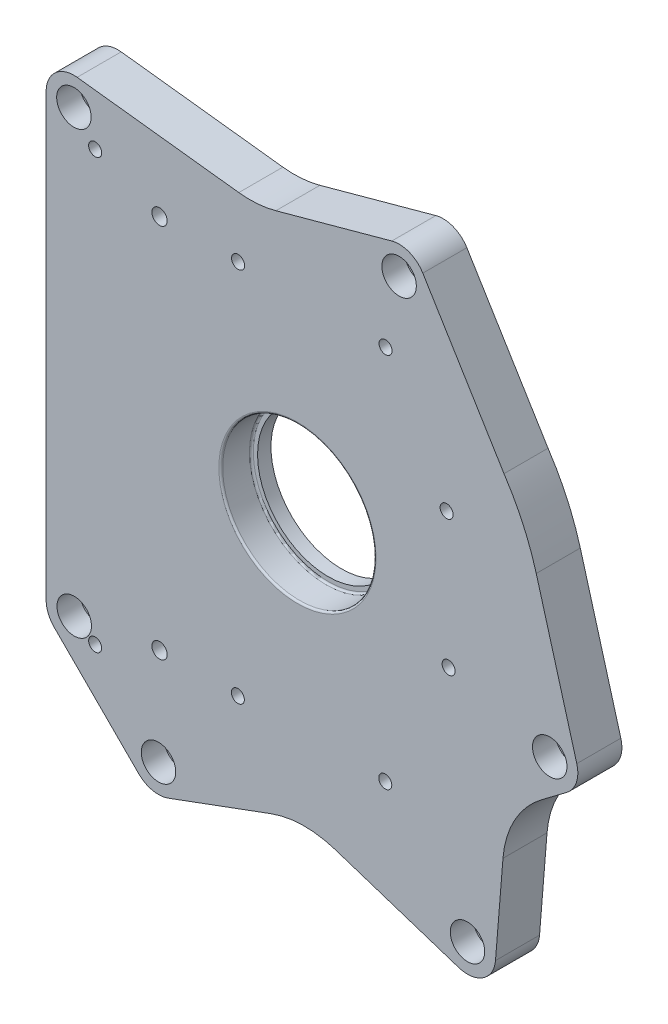
SolidWorks part; units mm, degrees
material "6061-T6 (SS)"
ref_plane "Front Plane" through (0, 0, 0) normal (0, 0, 1) x (1, 0, 0)
ref_plane "Top Plane" through (0, 0, 0) normal (0, 1, 0) x (1, 0, 0)
ref_plane "Right Plane" through (0, 0, 0) normal (1, 0, 0) x (0, 0, -1)
sketch "Sketch1" plane through (0, 0, 0) normal (0, 0, 1) x (1, 0, 0)
  line L0 (84.2211, -163.4901) -> (2.6993, -136.8316)
  line L1 (-67.4584, -162.7302) -> (2.6993, -136.8316)
  line L2 (-82.9108, -159.3414) -> (-126.9141, -115.3364)
  line L3 (140.5448, -56.1387) -> (109.1493, -79.774)
  line L4 (103.4012, -150.7323) -> (109.1493, -79.774)
  line L5 (145.8454, -40.4558) -> (124.6838, 34.9416)
  line L6 (65.4504, 141.1198) -> (107.841, 71.6428)
  line L9 (49.2431, 147.5528) -> (-20.7968, 128.3749)
  line L13 (-115.0226, 139.4368) -> (-20.7968, 128.3749)
  line L14 (-131.2133, 125.0355) -> (-131.2102, -104.9645)
  arc A2 (-115.0226, 139.4368) -> (-131.2133, 125.0355) centre (-116.7133, 125.0357) ccw
  circle A3 centre (-116.7133, 125.0357) radius 3.5 construction
  arc A6 (65.4504, 141.1198) -> (49.2431, 147.5528) centre (53.0725, 133.5676) ccw
  circle A7 centre (-76.5534, 103.7539) radius 2.5 construction
  arc A9 (-131.2102, -104.9645) -> (-126.9141, -115.3364) centre (-116.5415, -104.9643) ccw
  circle A10 centre (-116.5415, -104.9643) radius 3.5 construction
  arc A12 (-82.9108, -159.3414) -> (-67.4584, -162.7302) centre (-72.5383, -148.9692) ccw
  circle A13 centre (-72.5383, -148.9692) radius 3.5 construction
  arc A15 (84.2211, -163.4901) -> (103.4012, -150.7323) centre (88.7803, -149.548) ccw
  arc A17 (140.5448, -56.1387) -> (145.8454, -40.4558) centre (131.7224, -44.4197) ccw
  circle A18 centre (59.1026, -114.9804) radius 2.5 construction
  circle A23 centre (88.7803, -149.548) radius 3.5 construction
  circle A27 centre (131.7224, -44.4197) radius 3.5 construction
  arc A30 (124.6838, 34.9416) -> (107.841, 71.6428) centre (-0.017, -0.0702) ccw
  circle A31 centre (53.0725, 133.5676) radius 3.5 construction
  dimension "D1" = 14.5
  dimension "D2" = 7
  dimension "D3" = 5
extrude "Boss-Extrude1" add sketch "Sketch1" along normal blind 23 contours L5 A30 L6 A6 L9 L13 A2 L14 A9 L2 A12 L1 L0 A15 L4 L3 A17 A31 A3 A7 A10 A13 A18 A23 A27
fillet "Fillet2" radius 50.8 3 edges at (-20.7968, 128.3749, 11.5) (109.1493, -79.774, 11.5) (2.6993, -136.8316, 11.5)
sketch "Sketch2" plane through (0, 0, 23) normal (0, 0, -1) x (-1, 0, 0)
  circle A0 centre (0, 0) radius 40.05
  dimension "D1" = 80.1
extrude "Cut-Extrude1" cut sketch "Sketch2" along normal blind 16
sketch "Sketch5" plane through (0, 0, 23) normal (0, 0, -1) x (-1, 0, 0)
  circle A0 centre (0, 0) radius 36.83
  dimension "D1" = 73.66
extrude "Cut-Extrude2" cut sketch "Sketch5" along normal blind 25.4
sketch "Sketch6" [suppressed] plane through (0, 0, 0) normal (0, 0, 1) x (1, 0, 0)
  circle A0 centre (0, 0) radius 50.8 construction
  point P14 (0, 0)
  dimension "D2" = 101.6
fillet "Fillet5" radius 1 1 edges at (-40.05, 0, 23)
fillet "Fillet6" radius 1 1 edges at (-40.05, 0, 7)
sketch "Sketch43" plane through (0, 0, 23) normal (0, 0, 1) x (1, 0, 0)
  line L13 (0, 0) -> (150.4649, 0) construction
  line L14 (-31.12, -98.35) -> (-105.6166, -112.2929) construction
  line L15 (-31, 98) -> (-105.6166, 111.6261) construction
  line L16 (-105.6166, -112.2929) -> (-105.6166, 111.6261) construction
  line L17 (0, 0) -> (-105.6166, 111.6261) construction
  line L18 (-31, 98) -> (0, 0) construction
  line L19 (0, 0) -> (46, 97.92) construction
  line L20 (77.9, 39.75) -> (0, 0) construction
  line L21 (0, 0) -> (-72, -98.1221) construction
  line L22 (0, 0) -> (78.925, -30.46) construction
  line L23 (45.85, -98.52) -> (0, 0) construction
  line L24 (0, 0) -> (-72, 97.9779) construction
  line L25 (0, 0) -> (-31.12, -98.35) construction
  line L26 (-105.6166, -112.2929) -> (0, 0) construction
  circle A8 centre (0, 0) radius 46.4211 construction
  circle A12 centre (-46.643, -71.23) radius 11.3319 construction
  circle A13 centre (-72, 97.9779) radius 3.9701
  circle A14 centre (-72, -98.1221) radius 3.9701
  circle A15 centre (-105.6166, 111.6261) radius 3
  circle A16 centre (-31, 98) radius 3
  circle A17 centre (46, 97.92) radius 3
  circle A18 centre (77.9, 39.75) radius 3
  circle A19 centre (78.925, -30.46) radius 3
  circle A20 centre (45.85, -98.52) radius 3
  circle A21 centre (-31.12, -98.35) radius 3
  circle A22 centre (-105.6166, -112.2929) radius 3
  circle A23 centre (0, 0) radius 36.83 construction
  dimension "D2" = 45.85
  dimension "D3" = 31.12
  dimension "D1" = 98.52
  dimension "D4" = 98.35
  dimension "D5" = 98.1221
  dimension "D6" = 72
  dimension "D7" = 105.6166
  dimension "D8" = 105.6166
  dimension "D9" = 72
  dimension "D10" = 31
  dimension "D11" = 46
  dimension "D12" = 77.9
  dimension "D13" = 78.925
  dimension "D14" = 39.75
  dimension "D15" = 30.46
  dimension "D16" = 97.92
  dimension "D17" = 98
  dimension "D18" = 97.9779
  dimension "D19" = 111.6261
  dimension "D20" = 112.2929
  dimension "D21" = 196.1
  dimension "D22" = 7.9403
  dimension "D23" = 6
sketch "Sketch59" plane through (0, 0, 23) normal (0, 0, 1) x (1, 0, 0)
  line L0 (145.8454, -40.4558) -> (124.6838, 34.9416) construction
  line L1 (140.5448, -56.1387) -> (127.387, -66.0442) construction
  line L2 (103.4012, -150.7323) -> (107.3061, -102.5275) construction
  line L3 (84.2211, -163.4901) -> (19.4993, -142.3254) construction
  line L4 (-67.4584, -162.7302) -> (-13.8824, -142.9527) construction
  line L5 (-82.9108, -159.3414) -> (-126.9141, -115.3364) construction
  line L6 (65.4504, 141.1198) -> (107.841, 71.6428) construction
  line L7 (49.2431, 147.5528) -> (-11.269, 130.9837) construction
  line L8 (-115.0226, 139.4368) -> (-30.608, 129.5267) construction
  line L9 (-131.2133, 125.0355) -> (-131.2102, -104.9645) construction
  line L10 (145.8454, -40.4558) -> (124.6838, 34.9416)
  line L11 (140.5448, -56.1387) -> (127.387, -66.0442)
  line L12 (103.4012, -150.7323) -> (107.3061, -102.5275)
  line L13 (84.2211, -163.4901) -> (19.4993, -142.3254)
  line L14 (-67.4584, -162.7302) -> (-13.8824, -142.9527)
  line L15 (-82.9108, -159.3414) -> (-126.9141, -115.3364)
  line L16 (65.4504, 141.1198) -> (107.841, 71.6428)
  line L17 (49.2431, 147.5528) -> (-11.269, 130.9837)
  line L18 (-115.0226, 139.4368) -> (-30.608, 129.5267)
  line L19 (-131.2133, 125.0355) -> (-131.2102, -104.9645)
  line L30 (49.2431, 147.5528) -> (-20.7968, 128.3749)
  line L31 (107.841, 71.6428) -> (65.4504, 141.1198)
  line L32 (145.8454, -40.4558) -> (124.6838, 34.9416)
  line L33 (109.1493, -79.774) -> (140.5448, -56.1387)
  line L34 (103.4012, -150.7323) -> (109.1493, -79.774)
  line L35 (2.6993, -136.8316) -> (84.2211, -163.4901)
  line L36 (-67.4584, -162.7302) -> (2.6993, -136.8316)
  line L37 (-126.9141, -115.3364) -> (-82.9108, -159.3414)
  line L38 (-131.2133, 125.0355) -> (-131.2102, -104.9645)
  line L39 (-20.7968, 128.3749) -> (-115.0226, 139.4368)
  line L40 (49.2431, 147.5528) -> (-20.7968, 128.3749)
  line L41 (107.841, 71.6428) -> (65.4504, 141.1198)
  line L42 (145.8454, -40.4558) -> (124.6838, 34.9416)
  line L43 (109.1493, -79.774) -> (140.5448, -56.1387)
  line L44 (103.4012, -150.7323) -> (109.1493, -79.774)
  line L45 (2.6993, -136.8316) -> (84.2211, -163.4901)
  line L46 (-67.4584, -162.7302) -> (2.6993, -136.8316)
  line L47 (-126.9141, -115.3364) -> (-82.9108, -159.3414)
  line L48 (-131.2133, 125.0355) -> (-131.2102, -104.9645)
  line L49 (-20.7968, 128.3749) -> (-115.0226, 139.4368)
  arc A0 (124.6838, 34.9416) -> (107.841, 71.6428) centre (-0.017, -0.0702) ccw construction
  arc A1 (140.5448, -56.1387) -> (145.8454, -40.4558) centre (131.7224, -44.4197) ccw construction
  arc A2 (127.387, -66.0442) -> (107.3061, -102.5275) centre (157.9402, -106.6292) ccw construction
  arc A3 (84.2211, -163.4901) -> (103.4012, -150.7323) centre (88.7803, -149.548) ccw construction
  arc A4 (19.4993, -142.3254) -> (-13.8824, -142.9527) centre (3.7099, -190.6093) ccw construction
  arc A5 (-82.9108, -159.3414) -> (-67.4584, -162.7302) centre (-72.5383, -148.9692) ccw construction
  arc A6 (-131.2102, -104.9645) -> (-126.9141, -115.3364) centre (-116.5415, -104.9643) ccw construction
  arc A7 (65.4504, 141.1198) -> (49.2431, 147.5528) centre (53.0725, 133.5676) ccw construction
  arc A8 (-30.608, 129.5267) -> (-11.269, 130.9837) centre (-24.6849, 179.9802) ccw construction
  arc A9 (-115.0226, 139.4368) -> (-131.2133, 125.0355) centre (-116.7133, 125.0357) ccw construction
  arc A10 (124.6838, 34.9416) -> (107.841, 71.6428) centre (-0.017, -0.0702) ccw
  arc A11 (140.5448, -56.1387) -> (145.8454, -40.4558) centre (131.7224, -44.4197) ccw
  arc A12 (127.387, -66.0442) -> (107.3061, -102.5275) centre (157.9402, -106.6292) ccw
  arc A13 (84.2211, -163.4901) -> (103.4012, -150.7323) centre (88.7803, -149.548) ccw
  arc A14 (19.4993, -142.3254) -> (-13.8824, -142.9527) centre (3.7099, -190.6093) ccw
  arc A15 (-82.9108, -159.3414) -> (-67.4584, -162.7302) centre (-72.5383, -148.9692) ccw
  arc A16 (-131.2102, -104.9645) -> (-126.9141, -115.3364) centre (-116.5415, -104.9643) ccw
  arc A17 (65.4504, 141.1198) -> (49.2431, 147.5528) centre (53.0725, 133.5676) ccw
  arc A18 (-30.608, 129.5267) -> (-11.269, 130.9837) centre (-24.6849, 179.9802) ccw
  arc A19 (-115.0226, 139.4368) -> (-131.2133, 125.0355) centre (-116.7133, 125.0357) ccw
  circle A20 centre (-116.7133, 125.0357) radius 3.5 construction
  circle A21 centre (-76.5534, 103.7539) radius 2.5 construction
  circle A22 centre (-116.5415, -104.9643) radius 3.5 construction
  circle A23 centre (-72.5383, -148.9692) radius 3.5 construction
  circle A24 centre (59.1026, -114.9804) radius 2.5 construction
  circle A25 centre (88.7803, -149.548) radius 3.5 construction
  circle A26 centre (131.7224, -44.4197) radius 3.5 construction
  arc A27 (65.4504, 141.1198) -> (49.2431, 147.5528) centre (53.0725, 133.5676) ccw
  arc A28 (124.6838, 34.9416) -> (107.841, 71.6428) centre (-0.017, -0.0702) ccw
  arc A29 (140.5448, -56.1387) -> (145.8454, -40.4558) centre (131.7224, -44.4197) ccw
  arc A30 (84.2211, -163.4901) -> (103.4012, -150.7323) centre (88.7803, -149.548) ccw
  arc A31 (-82.9108, -159.3414) -> (-67.4584, -162.7302) centre (-72.5383, -148.9692) ccw
  arc A32 (-131.2102, -104.9645) -> (-126.9141, -115.3364) centre (-116.5415, -104.9643) ccw
  arc A33 (-115.0226, 139.4368) -> (-131.2133, 125.0355) centre (-116.7133, 125.0357) ccw
  arc A34 (65.4504, 141.1198) -> (49.2431, 147.5528) centre (53.0725, 133.5676) ccw
  arc A35 (124.6838, 34.9416) -> (107.841, 71.6428) centre (-0.017, -0.0702) ccw
  arc A36 (140.5448, -56.1387) -> (145.8454, -40.4558) centre (131.7224, -44.4197) ccw
  arc A37 (84.2211, -163.4901) -> (103.4012, -150.7323) centre (88.7803, -149.548) ccw
  arc A38 (-82.9108, -159.3414) -> (-67.4584, -162.7302) centre (-72.5383, -148.9692) ccw
  arc A39 (-131.2102, -104.9645) -> (-126.9141, -115.3364) centre (-116.5415, -104.9643) ccw
  arc A40 (-115.0226, 139.4368) -> (-131.2133, 125.0355) centre (-116.7133, 125.0357) ccw
  circle A41 centre (53.0725, 133.5676) radius 3.5 construction
  dimension "D1" = 0
hole_wizard "CBORE for M10 SHCS7" positions "Sketch62" profile "Sketch63" counterbore size "M10" standard "ANSI Metric" end condition through all
sketch "Sketch62" plane through (0, 0, 23) normal (0, 0, 1) x (1, 0, 0)
  point P0 (-116.7133, 125.0357)
  point P3 (-116.5415, -104.9643)
  point P7 (-72.5383, -148.9692)
  point P10 (53.0725, 133.5676)
  point P13 (131.7224, -44.4197)
  point P16 (88.7803, -149.548)
sketch "Sketch63" plane through (-116.7133, 125.0357, 23) normal (1, 0, 0) x (0, -1, 0)
  line L0 (0, 0) -> (0, 23)
  line L1 (0, 23) -> (5.25, 23)
  line L3 (5.25, 23) -> (5.25, 12)
  line L4 (5.25, 12) -> (9, 12)
  line L5 (9, 12) -> (9, 0)
  line L7 (9, 0) -> (0, 0)
  line L11 (0, -6.35) -> (0, 107.95) construction
  dimension "Thru Hole Dia." = 10.5
  dimension "Thru Hole Depth" = 23
  dimension "C'Bore Dia." = 18
  dimension "C'Bore Depth" = 12
hole_wizard "Tap Drill for M8x1.25 Tap2" positions "Sketch66" profile "Sketch67" hole size "M8x1.25" standard "ANSI Metric" end condition through all
sketch "Sketch66" plane through (0, 0, 23) normal (0, 0, 1) x (1, 0, 0)
  point P0 (46, 97.92)
  point P3 (-31, 98)
  point P6 (-105.6166, 111.6261)
  point P9 (-105.6166, -112.2929)
  point P12 (-31.12, -98.35)
  point P15 (45.85, -98.52)
  point P18 (78.925, -30.46)
  point P21 (77.9, 39.75)
sketch "Sketch67" plane through (46, 97.92, 23) normal (1, 0, 0) x (0, -1, 0)
  line L0 (0, 0) -> (0, 23)
  line L1 (0, 23) -> (3.4, 23)
  line L2 (3.4, 23) -> (3.4, 0)
  line L5 (3.4, 0) -> (0, 0)
  line L11 (0, -6.35) -> (0, 107.95) construction
  dimension "Thru Hole Dia." = 6.8
  dimension "Thru Hole Depth" = 23
hole_wizard "Ø8.0mm Dowel Hole1" positions "Sketch70" profile "Sketch71" hole size "Ø8.0" standard "ANSI Metric"
sketch "Sketch70" plane through (0, 0, 23) normal (0, 0, 1) x (1, 0, 0)
  point P0 (-72, 97.9779)
  point P3 (-72, -98.1221)
sketch "Sketch71" plane through (-72, 97.9779, 23) normal (1, 0, 0) x (0, -1, 0)
  line L0 (0, 0) -> (0, 11.4034)
  line L1 (0, 11.4034) -> (4, 9)
  line L2 (4, 9) -> (4, 0)
  line L5 (4, 0) -> (0, 0)
  line L10 (0, 11.4034) -> (-4, 9) construction
  line L11 (0, -6.35) -> (0, 107.95) construction
  dimension "Hole Dia." = 8
  dimension "Hole Depth" = 9
  dimension "Drill Angle" = 118
hole_wizard "Ø10.0mm Dowel Hole3" positions "Sketch72" profile "Sketch73" hole size "Ø10.0" standard "ANSI Metric"
sketch "Sketch72" plane through (0, 0, 0) normal (0, 0, -1) x (-1, 0, 0)
  point P0 (76.5534, 103.7539)
  point P3 (-59.1026, -114.9804)
sketch "Sketch73" plane through (-76.5534, 103.7539, 0) normal (1, 0, 0) x (0, 1, 0)
  line L0 (0, 0) -> (0, 13.0043)
  line L1 (0, 13.0043) -> (5, 10)
  line L2 (5, 10) -> (5, 0)
  line L5 (5, 0) -> (0, 0)
  line L10 (0, 13.0043) -> (-5, 10) construction
  line L11 (0, -6.35) -> (0, 107.95) construction
  dimension "Hole Dia." = 10
  dimension "Hole Depth" = 10
  dimension "Drill Angle" = 118
hole_wizard "CBORE for M10 SHCS9" positions "Sketch74" profile "Sketch75" counterbore size "M10" standard "ANSI Metric" end condition through all
sketch "Sketch74" plane through (0, 0, 23) normal (0, 0, 1) x (1, 0, 0)
  point P0 (53.0725, 133.5676)
  point P3 (131.7224, -44.4197)
  point P6 (88.7803, -149.548)
  point P9 (-116.7133, 125.0357)
  point P12 (-116.5415, -104.9643)
  point P15 (-72.5383, -148.9692)
  point P18 (-116.7133, 125.0357)
  point P21 (-116.5415, -104.9643)
  point P24 (-72.5383, -148.9692)
sketch "Sketch75" plane through (53.0725, 133.5676, 23) normal (1, 0, 0) x (0, -1, 0)
  line L0 (0, 0) -> (0, 23)
  line L1 (0, 23) -> (5.25, 23)
  line L3 (5.25, 23) -> (5.25, 10)
  line L4 (5.25, 10) -> (9, 10)
  line L5 (9, 10) -> (9, 0)
  line L7 (9, 0) -> (0, 0)
  line L11 (0, -6.35) -> (0, 107.95) construction
  dimension "Thru Hole Dia." = 10.5
  dimension "Thru Hole Depth" = 23
  dimension "C'Bore Dia." = 18
  dimension "C'Bore Depth" = 10
